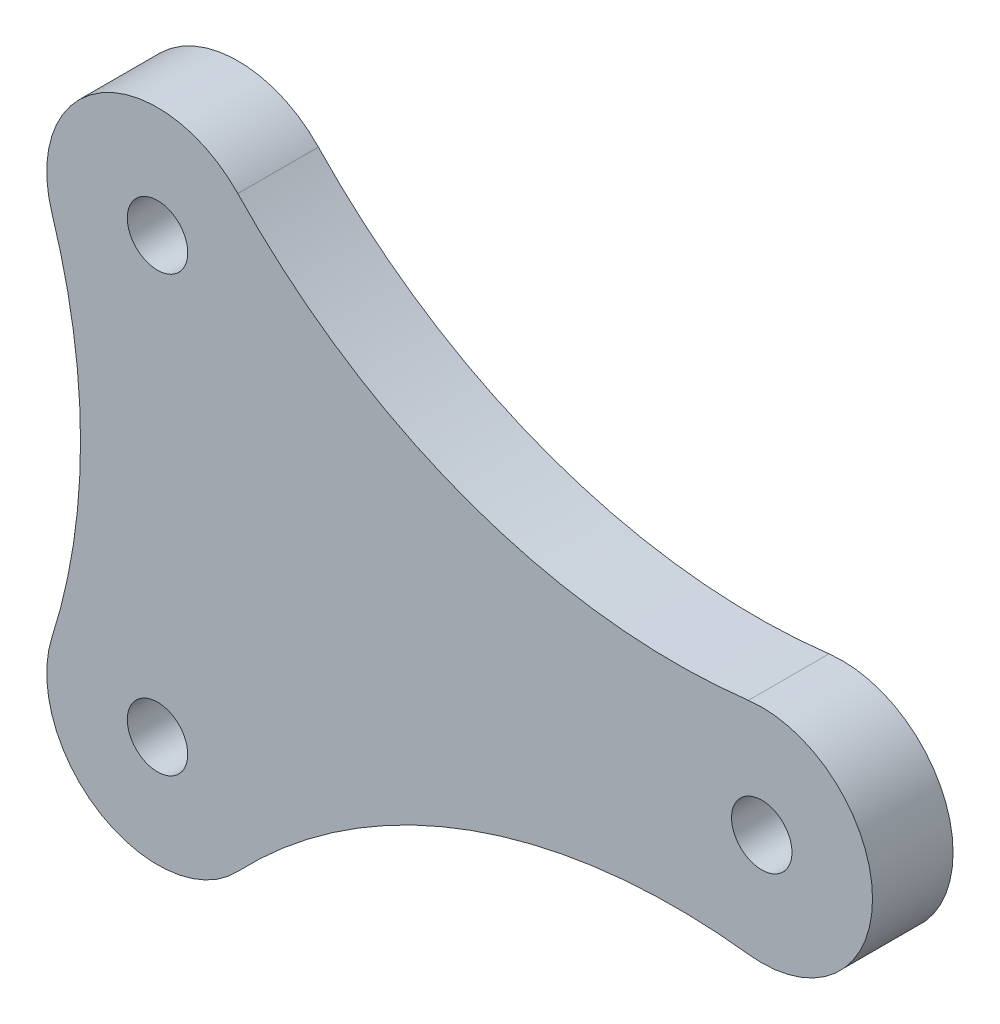
SolidWorks part; units mm, degrees
ref_plane "Front Plane" through (0, 0, 0) normal (0, 0, 1) x (1, 0, 0)
ref_plane "Top Plane" through (0, 0, 0) normal (0, 1, 0) x (1, 0, 0)
ref_plane "Right Plane" through (0, 0, 0) normal (1, 0, 0) x (0, 0, -1)
sketch "Sketch1" plane through (0, 0, 0) normal (0, 0, 1) x (1, 0, 0)
  line L0 (0, 21.57) -> (0, 0) construction
  circle A0 centre (0, 0) radius 1.5
  circle A1 centre (0, 21.57) radius 1.5
  circle A2 centre (30, 10.785) radius 1.5
  circle A6 centre (0, 21.57) radius 5.5
  circle A7 centre (30, 10.785) radius 5.5
  circle A8 centre (0, 0) radius 5.5
  arc A9 (-5.24, 19.8991) -> (-5.24, 1.6709) centre (-33.8221, 10.785) cw
  arc A10 (3.9865, 25.3592) -> (29.3386, 16.2451) centre (25.731, 46.0274) ccw
  arc A11 (3.9865, -3.7892) -> (29.3386, 5.3249) centre (25.731, -24.4574) cw
  point P7 (0, 10.785)
  dimension "D3" = 3
  dimension "D4" = 4
  dimension "D5" = 30
  dimension "D1" = 30
  dimension "D2" = 21.57
extrude "Boss-Extrude1" add sketch "Sketch1" along normal blind 4
